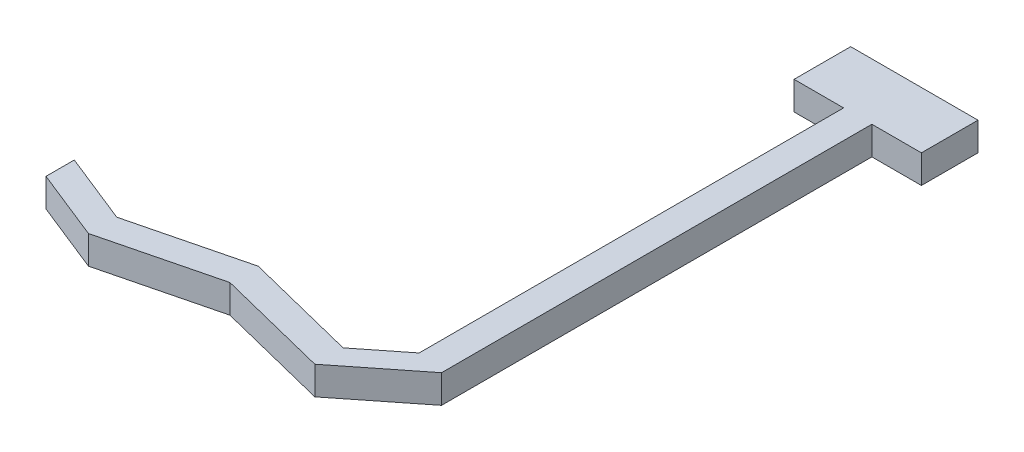
SolidWorks part; units mm, degrees
ref_plane "Front Plane" through (0, 0, 0) normal (0, 0, 1) x (1, 0, 0)
ref_plane "Top Plane" through (0, 0, 0) normal (0, 1, 0) x (1, 0, 0)
ref_plane "Right Plane" through (0, 0, 0) normal (1, 0, 0) x (0, 0, -1)
sketch "Sketch1" plane through (0, 0, 0) normal (0, 1, 0) x (1, 0, 0)
  line L0 (0, 0) -> (0, 30.416)
  line L1 (0, 30.416) -> (3.5, 30.416)
  line L2 (3.5, 30.416) -> (3.5, 34.416)
  line L3 (3.5, 34.416) -> (-5.5, 34.416)
  line L4 (-5.5, 34.416) -> (-5.5, 30.416)
  line L5 (-5.5, 30.416) -> (-2, 30.416)
  line L6 (-2, 30.416) -> (-2, 0.416)
  line L7 (-2, 0.416) -> (-5, -1.9599)
  line L8 (-5, -1.9599) -> (-13, 0.0401)
  line L9 (-13, 0.0401) -> (-21, -1.9599)
  line L10 (-21, -1.9599) -> (-26, 0.0401)
  line L11 (-26, 0.0401) -> (-26, -1.9599)
  line L12 (-26, -1.9599) -> (-21, -3.9599)
  line L13 (-21, -3.9599) -> (-13, -1.9599)
  line L14 (-13, -1.9599) -> (-5, -3.9599)
  line L15 (-5, -3.9599) -> (0, 0)
  point P7 (-18.4932, -0.4348)
  point P18 (-25.7103, -2.4687)
  point P19 (-12.2603, -2.1406)
  point P20 (0, 0)
  point P21 (-25.6119, -2.3047)
  point P22 (0, 0)
  point P23 (-18.6573, 5.8965)
  point P24 (0, 0)
  point P25 (-19.5102, 1.8571)
  point P26 (0, 0)
  point P27 (-16.7546, -2.1429)
  point P28 (0, 0)
  point P29 (-13.835, -2.1429)
  point P30 (0, 0)
  point P31 (-14.5567, -0.9597)
  point P32 (-2.0844, 1.0403)
  point P33 (-30.1183, -1.9524)
  point P34 (-34.2744, -0.4233)
  point P35 (5.6004, 10.9079)
  point P36 (-1.9173, 2.2864)
  point P37 (-11.8051, -4.5861)
  point P38 (-22.5072, -2.4273)
  point P39 (-1.4704, 0.742)
  point P40 (-13, -1.0287)
  point P41 (-7.1263, 10.8643)
  point P42 (-1.5744, 0.6886)
  point P43 (-2.7488, -0.801)
  point P44 (-4, -3.1031)
  point P45 (-5, -1.255)
  point P46 (0, 0)
  point P47 (-5.5, 11.0723)
  point P48 (-5.5, 13.8793)
  point P49 (0, 0)
  point P50 (-5, -5.601)
  point P51 (-5, -1.9599)
  dimension "D1" = 2
  dimension "D2" = 5
  dimension "D3" = 16
  dimension "D4" = 5
  dimension "D5" = 9
  dimension "D6" = 4
  dimension "D7" = 2
  dimension "D8" = 30
extrude "Boss-Extrude1" add sketch "Sketch1" along normal blind 2
